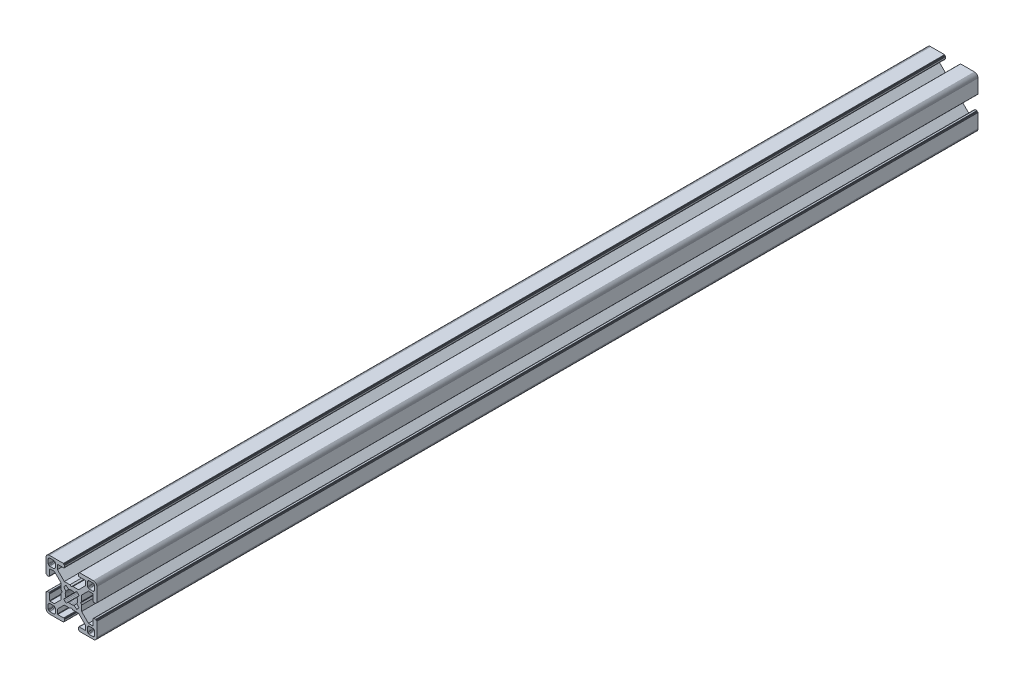
SolidWorks part; units mm, degrees
ref_plane "Front Plane" through (0, 0, 0) normal (0, 0, 1) x (1, 0, 0)
ref_plane "Top Plane" through (0, 0, 0) normal (0, 1, 0) x (1, 0, 0)
ref_plane "Right Plane" through (0, 0, 0) normal (1, 0, 0) x (0, 0, -1)
ref_plane "Plane1" through (0, 0, 0) normal (0, 0, 1) x (1, 0, 0)
sketch "Sketch1" plane through (0, 0, 0) normal (0, 0, 1) x (1, 0, 0)
  line L0 (28.3473, 29.9696) -> (28, 30)
  line L1 (28, 30) -> (19.75, 30)
  line L2 (19.75, 30) -> (19.7153, 29.997)
  line L3 (19.7153, 29.997) -> (19.6816, 29.9879)
  line L4 (19.6816, 29.9879) -> (19.65, 29.9732)
  line L5 (19.65, 29.9732) -> (19.6214, 29.9532)
  line L6 (19.6214, 29.9532) -> (19.5968, 29.9286)
  line L7 (19.5968, 29.9286) -> (19.5768, 29.9)
  line L8 (19.5768, 29.9) -> (19.5621, 29.8684)
  line L9 (19.5621, 29.8684) -> (19.553, 29.8347)
  line L10 (19.553, 29.8347) -> (19.55, 29.8)
  line L11 (19.55, 29.8) -> (19.55, 29.7)
  line L12 (19.55, 29.7) -> (19.547, 29.6653)
  line L13 (19.547, 29.6653) -> (19.5379, 29.6316)
  line L14 (19.5379, 29.6316) -> (19.5232, 29.6)
  line L15 (19.5232, 29.6) -> (19.5032, 29.5714)
  line L16 (19.5032, 29.5714) -> (19.4786, 29.5468)
  line L17 (19.4786, 29.5468) -> (19.45, 29.5268)
  line L18 (19.45, 29.5268) -> (19.4184, 29.5121)
  line L19 (19.4184, 29.5121) -> (19.3847, 29.503)
  line L20 (19.3847, 29.503) -> (19.35, 29.5)
  line L21 (19.35, 29.5) -> (19.25, 29.5)
  line L22 (19.25, 29.5) -> (19.2153, 29.497)
  line L23 (19.2153, 29.497) -> (19.1816, 29.4879)
  line L24 (19.1816, 29.4879) -> (19.15, 29.4732)
  line L25 (19.15, 29.4732) -> (19.1214, 29.4532)
  line L26 (19.1214, 29.4532) -> (19.0968, 29.4286)
  line L27 (19.0968, 29.4286) -> (19.0768, 29.4)
  line L28 (19.0768, 29.4) -> (19.0621, 29.3684)
  line L29 (19.0621, 29.3684) -> (19.053, 29.3347)
  line L30 (19.053, 29.3347) -> (19.05, 29.3)
  line L31 (19.05, 29.3) -> (19.05, 28.4)
  line L32 (19.05, 28.4) -> (19.0591, 28.2958)
  line L33 (19.0591, 28.2958) -> (19.0862, 28.1948)
  line L34 (19.0862, 28.1948) -> (19.1304, 28.1)
  line L35 (19.1304, 28.1) -> (19.1904, 28.0143)
  line L36 (19.1904, 28.0143) -> (19.2643, 27.9404)
  line L37 (19.2643, 27.9404) -> (19.35, 27.8804)
  line L38 (19.35, 27.8804) -> (19.4448, 27.8362)
  line L39 (19.4448, 27.8362) -> (19.5458, 27.8091)
  line L40 (19.5458, 27.8091) -> (19.65, 27.8)
  line L41 (19.65, 27.8) -> (23.05, 27.8)
  line L42 (23.05, 27.8) -> (23.0847, 27.7969)
  line L43 (23.0847, 27.7969) -> (23.1184, 27.7879)
  line L44 (23.1184, 27.7879) -> (23.15, 27.7732)
  line L45 (23.15, 27.7732) -> (23.1786, 27.7532)
  line L46 (23.1786, 27.7532) -> (23.2032, 27.7285)
  line L47 (23.2032, 27.7285) -> (23.2232, 27.7)
  line L48 (23.2232, 27.7) -> (23.2379, 27.6684)
  line L49 (23.2379, 27.6684) -> (23.247, 27.6347)
  line L50 (23.247, 27.6347) -> (23.25, 27.6)
  line L51 (23.25, 27.6) -> (23.25, 25.05)
  line L52 (23.25, 25.05) -> (19.2045, 21)
  line L53 (19.2045, 21) -> (15.9, 21)
  line L54 (15.9, 21) -> (15, 20.4848)
  line L55 (15, 20.4848) -> (14.1, 21)
  line L56 (14.1, 21) -> (10.7955, 21)
  line L57 (10.7955, 21) -> (7.9973, 23.8013)
  line L58 (7.9973, 23.8013) -> (6.75, 25.05)
  line L59 (6.75, 25.05) -> (6.75, 27.6)
  line L60 (6.75, 27.6) -> (6.753, 27.6347)
  line L61 (6.753, 27.6347) -> (6.7621, 27.6684)
  line L62 (6.7621, 27.6684) -> (6.7768, 27.7)
  line L63 (6.7768, 27.7) -> (6.7968, 27.7285)
  line L64 (6.7968, 27.7285) -> (6.8215, 27.7532)
  line L65 (6.8215, 27.7532) -> (6.85, 27.7732)
  line L66 (6.85, 27.7732) -> (6.8816, 27.7879)
  line L67 (6.8816, 27.7879) -> (6.9153, 27.7969)
  line L68 (6.9153, 27.7969) -> (6.95, 27.8)
  line L69 (6.95, 27.8) -> (10.35, 27.8)
  line L70 (10.35, 27.8) -> (10.4542, 27.8091)
  line L71 (10.4542, 27.8091) -> (10.5552, 27.8362)
  line L72 (10.5552, 27.8362) -> (10.65, 27.8804)
  line L73 (10.65, 27.8804) -> (10.7357, 27.9404)
  line L74 (10.7357, 27.9404) -> (10.8096, 28.0143)
  line L75 (10.8096, 28.0143) -> (10.8696, 28.1)
  line L76 (10.8696, 28.1) -> (10.9138, 28.1948)
  line L77 (10.9138, 28.1948) -> (10.9409, 28.2958)
  line L78 (10.9409, 28.2958) -> (10.95, 28.4)
  line L79 (10.95, 28.4) -> (10.95, 29.3)
  line L80 (10.95, 29.3) -> (10.947, 29.3347)
  line L81 (10.947, 29.3347) -> (10.938, 29.3684)
  line L82 (10.938, 29.3684) -> (10.9232, 29.4)
  line L83 (10.9232, 29.4) -> (10.9032, 29.4286)
  line L84 (10.9032, 29.4286) -> (10.8786, 29.4532)
  line L85 (10.8786, 29.4532) -> (10.85, 29.4732)
  line L86 (10.85, 29.4732) -> (10.8184, 29.4879)
  line L87 (10.8184, 29.4879) -> (10.7847, 29.497)
  line L88 (10.7847, 29.497) -> (10.75, 29.5)
  line L89 (10.75, 29.5) -> (10.65, 29.5)
  line L90 (10.65, 29.5) -> (10.6153, 29.503)
  line L91 (10.6153, 29.503) -> (10.5816, 29.5121)
  line L92 (10.5816, 29.5121) -> (10.55, 29.5268)
  line L93 (10.55, 29.5268) -> (10.5214, 29.5468)
  line L94 (10.5214, 29.5468) -> (10.4968, 29.5714)
  line L95 (10.4968, 29.5714) -> (10.4768, 29.6)
  line L96 (10.4768, 29.6) -> (10.4621, 29.6316)
  line L97 (10.4621, 29.6316) -> (10.453, 29.6653)
  line L98 (10.453, 29.6653) -> (10.45, 29.7)
  line L99 (10.45, 29.7) -> (10.45, 29.8)
  line L100 (10.45, 29.8) -> (10.447, 29.8347)
  line L101 (10.447, 29.8347) -> (10.4379, 29.8684)
  line L102 (10.4379, 29.8684) -> (10.4232, 29.9)
  line L103 (10.4232, 29.9) -> (10.4032, 29.9286)
  line L104 (10.4032, 29.9286) -> (10.3786, 29.9532)
  line L105 (10.3786, 29.9532) -> (10.35, 29.9732)
  line L106 (10.35, 29.9732) -> (10.3184, 29.9879)
  line L107 (10.3184, 29.9879) -> (10.2847, 29.997)
  line L108 (10.2847, 29.997) -> (10.25, 30)
  line L109 (10.25, 30) -> (2, 30)
  line L110 (2, 30) -> (1.6527, 29.9696)
  line L111 (1.6527, 29.9696) -> (1.316, 29.8794)
  line L112 (1.316, 29.8794) -> (1, 29.7321)
  line L113 (1, 29.7321) -> (0.7144, 29.5321)
  line L114 (0.7144, 29.5321) -> (0.4679, 29.2856)
  line L115 (0.4679, 29.2856) -> (0.2679, 29)
  line L116 (0.2679, 29) -> (0.1206, 28.684)
  line L117 (0.1206, 28.684) -> (0.0304, 28.3473)
  line L118 (0.0304, 28.3473) -> (0, 28)
  line L119 (0, 28) -> (0, 19.75)
  line L120 (0, 19.75) -> (0.003, 19.7153)
  line L121 (0.003, 19.7153) -> (0.0121, 19.6816)
  line L122 (0.0121, 19.6816) -> (0.0268, 19.65)
  line L123 (0.0268, 19.65) -> (0.0468, 19.6214)
  line L124 (0.0468, 19.6214) -> (0.0714, 19.5968)
  line L125 (0.0714, 19.5968) -> (0.1, 19.5768)
  line L126 (0.1, 19.5768) -> (0.1316, 19.5621)
  line L127 (0.1316, 19.5621) -> (0.1653, 19.553)
  line L128 (0.1653, 19.553) -> (0.2, 19.55)
  line L129 (0.2, 19.55) -> (0.3, 19.55)
  line L130 (0.3, 19.55) -> (0.3347, 19.547)
  line L131 (0.3347, 19.547) -> (0.3684, 19.5379)
  line L132 (0.3684, 19.5379) -> (0.4, 19.5232)
  line L133 (0.4, 19.5232) -> (0.4286, 19.5032)
  line L134 (0.4286, 19.5032) -> (0.4532, 19.4786)
  line L135 (0.4532, 19.4786) -> (0.4732, 19.45)
  line L136 (0.4732, 19.45) -> (0.4879, 19.4184)
  line L137 (0.4879, 19.4184) -> (0.497, 19.3847)
  line L138 (0.497, 19.3847) -> (0.5, 19.35)
  line L139 (0.5, 19.35) -> (0.5, 19.25)
  line L140 (0.5, 19.25) -> (0.503, 19.2153)
  line L141 (0.503, 19.2153) -> (0.5121, 19.1816)
  line L142 (0.5121, 19.1816) -> (0.5268, 19.15)
  line L143 (0.5268, 19.15) -> (0.5468, 19.1214)
  line L144 (0.5468, 19.1214) -> (0.5714, 19.0968)
  line L145 (0.5714, 19.0968) -> (0.6, 19.0768)
  line L146 (0.6, 19.0768) -> (0.6316, 19.0621)
  line L147 (0.6316, 19.0621) -> (0.6653, 19.053)
  line L148 (0.6653, 19.053) -> (0.7, 19.05)
  line L149 (0.7, 19.05) -> (1.6, 19.05)
  line L150 (1.6, 19.05) -> (1.7042, 19.0591)
  line L151 (1.7042, 19.0591) -> (1.8052, 19.0862)
  line L152 (1.8052, 19.0862) -> (1.9, 19.1304)
  line L153 (1.9, 19.1304) -> (1.9857, 19.1904)
  line L154 (1.9857, 19.1904) -> (2.0596, 19.2643)
  line L155 (2.0596, 19.2643) -> (2.1196, 19.35)
  line L156 (2.1196, 19.35) -> (2.1638, 19.4448)
  line L157 (2.1638, 19.4448) -> (2.1909, 19.5458)
  line L158 (2.1909, 19.5458) -> (2.2, 19.65)
  line L159 (2.2, 19.65) -> (2.2, 23.05)
  line L160 (2.2, 23.05) -> (2.203, 23.0847)
  line L161 (2.203, 23.0847) -> (2.2121, 23.1184)
  line L162 (2.2121, 23.1184) -> (2.2268, 23.15)
  line L163 (2.2268, 23.15) -> (2.2468, 23.1786)
  line L164 (2.2468, 23.1786) -> (2.2714, 23.2032)
  line L165 (2.2714, 23.2032) -> (2.3, 23.2232)
  line L166 (2.3, 23.2232) -> (2.3316, 23.2379)
  line L167 (2.3316, 23.2379) -> (2.3653, 23.247)
  line L168 (2.3653, 23.247) -> (2.4, 23.25)
  line L169 (2.4, 23.25) -> (4.95, 23.25)
  line L170 (4.95, 23.25) -> (7.9973, 20.2027)
  line L171 (7.9973, 20.2027) -> (8.9955, 19.2045)
  line L172 (8.9955, 19.2045) -> (8.9955, 15.9)
  line L173 (8.9955, 15.9) -> (9.5151, 15)
  line L174 (9.5151, 15) -> (8.9955, 14.1)
  line L175 (8.9955, 14.1) -> (8.9955, 10.7955)
  line L176 (8.9955, 10.7955) -> (4.95, 6.75)
  line L177 (4.95, 6.75) -> (2.4, 6.75)
  line L178 (2.4, 6.75) -> (2.3653, 6.753)
  line L179 (2.3653, 6.753) -> (2.3316, 6.7621)
  line L180 (2.3316, 6.7621) -> (2.3, 6.7768)
  line L181 (2.3, 6.7768) -> (2.2714, 6.7968)
  line L182 (2.2714, 6.7968) -> (2.2468, 6.8214)
  line L183 (2.2468, 6.8214) -> (2.2268, 6.85)
  line L184 (2.2268, 6.85) -> (2.2121, 6.8816)
  line L185 (2.2121, 6.8816) -> (2.203, 6.9153)
  line L186 (2.203, 6.9153) -> (2.2, 6.95)
  line L187 (2.2, 6.95) -> (2.2, 10.35)
  line L188 (2.2, 10.35) -> (2.1909, 10.4542)
  line L189 (2.1909, 10.4542) -> (2.1638, 10.5552)
  line L190 (2.1638, 10.5552) -> (2.1196, 10.65)
  line L191 (2.1196, 10.65) -> (2.0596, 10.7357)
  line L192 (2.0596, 10.7357) -> (1.9857, 10.8096)
  line L193 (1.9857, 10.8096) -> (1.9, 10.8696)
  line L194 (1.9, 10.8696) -> (1.8052, 10.9138)
  line L195 (1.8052, 10.9138) -> (1.7042, 10.9409)
  line L196 (1.7042, 10.9409) -> (1.6, 10.95)
  line L197 (1.6, 10.95) -> (0.7, 10.95)
  line L198 (0.7, 10.95) -> (0.6653, 10.9469)
  line L199 (0.6653, 10.9469) -> (0.6316, 10.9379)
  line L200 (0.6316, 10.9379) -> (0.6, 10.9232)
  line L201 (0.6, 10.9232) -> (0.5715, 10.9032)
  line L202 (0.5715, 10.9032) -> (0.5468, 10.8785)
  line L203 (0.5468, 10.8785) -> (0.5268, 10.85)
  line L204 (0.5268, 10.85) -> (0.5121, 10.8184)
  line L205 (0.5121, 10.8184) -> (0.503, 10.7847)
  line L206 (0.503, 10.7847) -> (0.5, 10.75)
  line L207 (0.5, 10.75) -> (0.5, 10.65)
  line L208 (0.5, 10.65) -> (0.497, 10.6153)
  line L209 (0.497, 10.6153) -> (0.4879, 10.5816)
  line L210 (0.4879, 10.5816) -> (0.4732, 10.55)
  line L211 (0.4732, 10.55) -> (0.4532, 10.5214)
  line L212 (0.4532, 10.5214) -> (0.4286, 10.4968)
  line L213 (0.4286, 10.4968) -> (0.4, 10.4768)
  line L214 (0.4, 10.4768) -> (0.3684, 10.4621)
  line L215 (0.3684, 10.4621) -> (0.3347, 10.453)
  line L216 (0.3347, 10.453) -> (0.3, 10.45)
  line L217 (0.3, 10.45) -> (0.2, 10.45)
  line L218 (0.2, 10.45) -> (0.1653, 10.447)
  line L219 (0.1653, 10.447) -> (0.1316, 10.4379)
  line L220 (0.1316, 10.4379) -> (0.1, 10.4232)
  line L221 (0.1, 10.4232) -> (0.0714, 10.4032)
  line L222 (0.0714, 10.4032) -> (0.0468, 10.3786)
  line L223 (0.0468, 10.3786) -> (0.0268, 10.35)
  line L224 (0.0268, 10.35) -> (0.0121, 10.3184)
  line L225 (0.0121, 10.3184) -> (0.003, 10.2847)
  line L226 (0.003, 10.2847) -> (0, 10.25)
  line L227 (0, 10.25) -> (0, 2)
  line L228 (0, 2) -> (0.0304, 1.6527)
  line L229 (0.0304, 1.6527) -> (0.1206, 1.316)
  line L230 (0.1206, 1.316) -> (0.2679, 1)
  line L231 (0.2679, 1) -> (0.4679, 0.7144)
  line L232 (0.4679, 0.7144) -> (0.7144, 0.4679)
  line L233 (0.7144, 0.4679) -> (1, 0.2679)
  line L234 (1, 0.2679) -> (1.316, 0.1206)
  line L235 (1.316, 0.1206) -> (1.6527, 0.0304)
  line L236 (1.6527, 0.0304) -> (2, 0)
  line L237 (2, 0) -> (10.25, 0)
  line L238 (10.25, 0) -> (10.2847, 0.003)
  line L239 (10.2847, 0.003) -> (10.3184, 0.0121)
  line L240 (10.3184, 0.0121) -> (10.35, 0.0268)
  line L241 (10.35, 0.0268) -> (10.3786, 0.0468)
  line L242 (10.3786, 0.0468) -> (10.4032, 0.0714)
  line L243 (10.4032, 0.0714) -> (10.4232, 0.1)
  line L244 (10.4232, 0.1) -> (10.4379, 0.1316)
  line L245 (10.4379, 0.1316) -> (10.447, 0.1653)
  line L246 (10.447, 0.1653) -> (10.45, 0.2)
  line L247 (10.45, 0.2) -> (10.45, 0.3)
  line L248 (10.45, 0.3) -> (10.453, 0.3347)
  line L249 (10.453, 0.3347) -> (10.4621, 0.3684)
  line L250 (10.4621, 0.3684) -> (10.4768, 0.4)
  line L251 (10.4768, 0.4) -> (10.4968, 0.4286)
  line L252 (10.4968, 0.4286) -> (10.5214, 0.4532)
  line L253 (10.5214, 0.4532) -> (10.55, 0.4732)
  line L254 (10.55, 0.4732) -> (10.5816, 0.4879)
  line L255 (10.5816, 0.4879) -> (10.6153, 0.497)
  line L256 (10.6153, 0.497) -> (10.65, 0.5)
  line L257 (10.65, 0.5) -> (10.75, 0.5)
  line L258 (10.75, 0.5) -> (10.7847, 0.503)
  line L259 (10.7847, 0.503) -> (10.8184, 0.5121)
  line L260 (10.8184, 0.5121) -> (10.85, 0.5268)
  line L261 (10.85, 0.5268) -> (10.8785, 0.5468)
  line L262 (10.8785, 0.5468) -> (10.9032, 0.5715)
  line L263 (10.9032, 0.5715) -> (10.9232, 0.6)
  line L264 (10.9232, 0.6) -> (10.9379, 0.6316)
  line L265 (10.9379, 0.6316) -> (10.9469, 0.6653)
  line L266 (10.9469, 0.6653) -> (10.95, 0.7)
  line L267 (10.95, 0.7) -> (10.95, 1.6)
  line L268 (10.95, 1.6) -> (10.9409, 1.7042)
  line L269 (10.9409, 1.7042) -> (10.9138, 1.8052)
  line L270 (10.9138, 1.8052) -> (10.8696, 1.9)
  line L271 (10.8696, 1.9) -> (10.8096, 1.9857)
  line L272 (10.8096, 1.9857) -> (10.7357, 2.0596)
  line L273 (10.7357, 2.0596) -> (10.65, 2.1196)
  line L274 (10.65, 2.1196) -> (10.5552, 2.1638)
  line L275 (10.5552, 2.1638) -> (10.4542, 2.1909)
  line L276 (10.4542, 2.1909) -> (10.35, 2.2)
  line L277 (10.35, 2.2) -> (6.95, 2.2)
  line L278 (6.95, 2.2) -> (6.9153, 2.203)
  line L279 (6.9153, 2.203) -> (6.8816, 2.212)
  line L280 (6.8816, 2.212) -> (6.85, 2.2268)
  line L281 (6.85, 2.2268) -> (6.8215, 2.2468)
  line L282 (6.8215, 2.2468) -> (6.7968, 2.2714)
  line L283 (6.7968, 2.2714) -> (6.7768, 2.3)
  line L284 (6.7768, 2.3) -> (6.7621, 2.3316)
  line L285 (6.7621, 2.3316) -> (6.753, 2.3653)
  line L286 (6.753, 2.3653) -> (6.75, 2.4)
  line L287 (6.75, 2.4) -> (6.75, 4.95)
  line L288 (6.75, 4.95) -> (9.7875, 7.9908)
  line L289 (9.7875, 7.9908) -> (10.7955, 9)
  line L290 (10.7955, 9) -> (14.1, 9)
  line L291 (14.1, 9) -> (15, 9.5151)
  line L292 (15, 9.5151) -> (15.9, 9)
  line L293 (15.9, 9) -> (19.2045, 9)
  line L294 (19.2045, 9) -> (20.2126, 7.9908)
  line L295 (20.2126, 7.9908) -> (23.25, 4.95)
  line L296 (23.25, 4.95) -> (23.25, 2.4)
  line L297 (23.25, 2.4) -> (23.247, 2.3653)
  line L298 (23.247, 2.3653) -> (23.2379, 2.3316)
  line L299 (23.2379, 2.3316) -> (23.2232, 2.3)
  line L300 (23.2232, 2.3) -> (23.2032, 2.2714)
  line L301 (23.2032, 2.2714) -> (23.1786, 2.2468)
  line L302 (23.1786, 2.2468) -> (23.15, 2.2268)
  line L303 (23.15, 2.2268) -> (23.1184, 2.212)
  line L304 (23.1184, 2.212) -> (23.0847, 2.203)
  line L305 (23.0847, 2.203) -> (23.05, 2.2)
  line L306 (23.05, 2.2) -> (19.65, 2.2)
  line L307 (19.65, 2.2) -> (19.5458, 2.1909)
  line L308 (19.5458, 2.1909) -> (19.4448, 2.1638)
  line L309 (19.4448, 2.1638) -> (19.35, 2.1196)
  line L310 (19.35, 2.1196) -> (19.2643, 2.0596)
  line L311 (19.2643, 2.0596) -> (19.1904, 1.9857)
  line L312 (19.1904, 1.9857) -> (19.1304, 1.9)
  line L313 (19.1304, 1.9) -> (19.0862, 1.8052)
  line L314 (19.0862, 1.8052) -> (19.0591, 1.7042)
  line L315 (19.0591, 1.7042) -> (19.05, 1.6)
  line L316 (19.05, 1.6) -> (19.05, 0.7)
  line L317 (19.05, 0.7) -> (19.053, 0.6653)
  line L318 (19.053, 0.6653) -> (19.0621, 0.6316)
  line L319 (19.0621, 0.6316) -> (19.0768, 0.6)
  line L320 (19.0768, 0.6) -> (19.0968, 0.5714)
  line L321 (19.0968, 0.5714) -> (19.1214, 0.5468)
  line L322 (19.1214, 0.5468) -> (19.15, 0.5268)
  line L323 (19.15, 0.5268) -> (19.1816, 0.5121)
  line L324 (19.1816, 0.5121) -> (19.2153, 0.503)
  line L325 (19.2153, 0.503) -> (19.25, 0.5)
  line L326 (19.25, 0.5) -> (19.35, 0.5)
  line L327 (19.35, 0.5) -> (19.3847, 0.497)
  line L328 (19.3847, 0.497) -> (19.4184, 0.4879)
  line L329 (19.4184, 0.4879) -> (19.45, 0.4732)
  line L330 (19.45, 0.4732) -> (19.4786, 0.4532)
  line L331 (19.4786, 0.4532) -> (19.5032, 0.4286)
  line L332 (19.5032, 0.4286) -> (19.5232, 0.4)
  line L333 (19.5232, 0.4) -> (19.5379, 0.3684)
  line L334 (19.5379, 0.3684) -> (19.547, 0.3347)
  line L335 (19.547, 0.3347) -> (19.55, 0.3)
  line L336 (19.55, 0.3) -> (19.55, 0.2)
  line L337 (19.55, 0.2) -> (19.553, 0.1653)
  line L338 (19.553, 0.1653) -> (19.5621, 0.1316)
  line L339 (19.5621, 0.1316) -> (19.5768, 0.1)
  line L340 (19.5768, 0.1) -> (19.5968, 0.0714)
  line L341 (19.5968, 0.0714) -> (19.6214, 0.0468)
  line L342 (19.6214, 0.0468) -> (19.65, 0.0268)
  line L343 (19.65, 0.0268) -> (19.6816, 0.0121)
  line L344 (19.6816, 0.0121) -> (19.7153, 0.003)
  line L345 (19.7153, 0.003) -> (19.75, 0)
  line L346 (19.75, 0) -> (28, 0)
  line L347 (28, 0) -> (28.3473, 0.0304)
  line L348 (28.3473, 0.0304) -> (28.684, 0.1206)
  line L349 (28.684, 0.1206) -> (29, 0.2679)
  line L350 (29, 0.2679) -> (29.2856, 0.4679)
  line L351 (29.2856, 0.4679) -> (29.5321, 0.7144)
  line L352 (29.5321, 0.7144) -> (29.7321, 1)
  line L353 (29.7321, 1) -> (29.8794, 1.316)
  line L354 (29.8794, 1.316) -> (29.9696, 1.6527)
  line L355 (29.9696, 1.6527) -> (30, 2)
  line L356 (30, 2) -> (30, 10.25)
  line L357 (30, 10.25) -> (29.997, 10.2847)
  line L358 (29.997, 10.2847) -> (29.988, 10.3184)
  line L359 (29.988, 10.3184) -> (29.9732, 10.35)
  line L360 (29.9732, 10.35) -> (29.9532, 10.3785)
  line L361 (29.9532, 10.3785) -> (29.9286, 10.4032)
  line L362 (29.9286, 10.4032) -> (29.9, 10.4232)
  line L363 (29.9, 10.4232) -> (29.8684, 10.4379)
  line L364 (29.8684, 10.4379) -> (29.8347, 10.447)
  line L365 (29.8347, 10.447) -> (29.8, 10.45)
  line L366 (29.8, 10.45) -> (29.7, 10.45)
  line L367 (29.7, 10.45) -> (29.6649, 10.4534)
  line L368 (29.6649, 10.4534) -> (29.6312, 10.4624)
  line L369 (29.6312, 10.4624) -> (29.5996, 10.4772)
  line L370 (29.5996, 10.4772) -> (29.5711, 10.4972)
  line L371 (29.5711, 10.4972) -> (29.5464, 10.5218)
  line L372 (29.5464, 10.5218) -> (29.5264, 10.5504)
  line L373 (29.5264, 10.5504) -> (29.5117, 10.582)
  line L374 (29.5117, 10.582) -> (29.5027, 10.6156)
  line L375 (29.5027, 10.6156) -> (29.4996, 10.6504)
  line L376 (29.4996, 10.6504) -> (29.4996, 10.7504)
  line L377 (29.4996, 10.7504) -> (29.497, 10.7847)
  line L378 (29.497, 10.7847) -> (29.4879, 10.8184)
  line L379 (29.4879, 10.8184) -> (29.4732, 10.85)
  line L380 (29.4732, 10.85) -> (29.4532, 10.8785)
  line L381 (29.4532, 10.8785) -> (29.4286, 10.9032)
  line L382 (29.4286, 10.9032) -> (29.4, 10.9232)
  line L383 (29.4, 10.9232) -> (29.3684, 10.9379)
  line L384 (29.3684, 10.9379) -> (29.3347, 10.9469)
  line L385 (29.3347, 10.9469) -> (29.3, 10.95)
  line L386 (29.3, 10.95) -> (28.4, 10.95)
  line L387 (28.4, 10.95) -> (28.2958, 10.9409)
  line L388 (28.2958, 10.9409) -> (28.1948, 10.9138)
  line L389 (28.1948, 10.9138) -> (28.1, 10.8696)
  line L390 (28.1, 10.8696) -> (28.0143, 10.8096)
  line L391 (28.0143, 10.8096) -> (27.9404, 10.7357)
  line L392 (27.9404, 10.7357) -> (27.8804, 10.65)
  line L393 (27.8804, 10.65) -> (27.8362, 10.5552)
  line L394 (27.8362, 10.5552) -> (27.8091, 10.4542)
  line L395 (27.8091, 10.4542) -> (27.8, 10.35)
  line L396 (27.8, 10.35) -> (27.8, 6.95)
  line L397 (27.8, 6.95) -> (27.797, 6.9153)
  line L398 (27.797, 6.9153) -> (27.7879, 6.8816)
  line L399 (27.7879, 6.8816) -> (27.7732, 6.85)
  line L400 (27.7732, 6.85) -> (27.7532, 6.8214)
  line L401 (27.7532, 6.8214) -> (27.7286, 6.7968)
  line L402 (27.7286, 6.7968) -> (27.7, 6.7768)
  line L403 (27.7, 6.7768) -> (27.6684, 6.7621)
  line L404 (27.6684, 6.7621) -> (27.6347, 6.753)
  line L405 (27.6347, 6.753) -> (27.6, 6.75)
  line L406 (27.6, 6.75) -> (25.05, 6.75)
  line L407 (25.05, 6.75) -> (23.8092, 7.9908)
  line L408 (23.8092, 7.9908) -> (21.0045, 10.7955)
  line L409 (21.0045, 10.7955) -> (21.0045, 14.1)
  line L410 (21.0045, 14.1) -> (20.4849, 15)
  line L411 (20.4849, 15) -> (21.0045, 15.9)
  line L412 (21.0045, 15.9) -> (21.0045, 19.2045)
  line L413 (21.0045, 19.2045) -> (25.05, 23.25)
  line L414 (25.05, 23.25) -> (27.6, 23.25)
  line L415 (27.6, 23.25) -> (27.6347, 23.247)
  line L416 (27.6347, 23.247) -> (27.6684, 23.2379)
  line L417 (27.6684, 23.2379) -> (27.7, 23.2232)
  line L418 (27.7, 23.2232) -> (27.7286, 23.2032)
  line L419 (27.7286, 23.2032) -> (27.7532, 23.1786)
  line L420 (27.7532, 23.1786) -> (27.7732, 23.15)
  line L421 (27.7732, 23.15) -> (27.7879, 23.1184)
  line L422 (27.7879, 23.1184) -> (27.797, 23.0847)
  line L423 (27.797, 23.0847) -> (27.8, 23.05)
  line L424 (27.8, 23.05) -> (27.8, 19.65)
  line L425 (27.8, 19.65) -> (27.8091, 19.5458)
  line L426 (27.8091, 19.5458) -> (27.8362, 19.4448)
  line L427 (27.8362, 19.4448) -> (27.8804, 19.35)
  line L428 (27.8804, 19.35) -> (27.9404, 19.2643)
  line L429 (27.9404, 19.2643) -> (28.0143, 19.1904)
  line L430 (28.0143, 19.1904) -> (28.1, 19.1304)
  line L431 (28.1, 19.1304) -> (28.1948, 19.0862)
  line L432 (28.1948, 19.0862) -> (28.2958, 19.0591)
  line L433 (28.2958, 19.0591) -> (28.4, 19.05)
  line L434 (28.4, 19.05) -> (29.3, 19.05)
  line L435 (29.3, 19.05) -> (29.3347, 19.053)
  line L436 (29.3347, 19.053) -> (29.3684, 19.0621)
  line L437 (29.3684, 19.0621) -> (29.4, 19.0768)
  line L438 (29.4, 19.0768) -> (29.4282, 19.0971)
  line L439 (29.4282, 19.0971) -> (29.4528, 19.1218)
  line L440 (29.4528, 19.1218) -> (29.4728, 19.1504)
  line L441 (29.4728, 19.1504) -> (29.4876, 19.182)
  line L442 (29.4876, 19.182) -> (29.4966, 19.2156)
  line L443 (29.4966, 19.2156) -> (29.4996, 19.2504)
  line L444 (29.4996, 19.2504) -> (29.4996, 19.3504)
  line L445 (29.4996, 19.3504) -> (29.5027, 19.3851)
  line L446 (29.5027, 19.3851) -> (29.5117, 19.4188)
  line L447 (29.5117, 19.4188) -> (29.5264, 19.4504)
  line L448 (29.5264, 19.4504) -> (29.5464, 19.4789)
  line L449 (29.5464, 19.4789) -> (29.5711, 19.5036)
  line L450 (29.5711, 19.5036) -> (29.5996, 19.5236)
  line L451 (29.5996, 19.5236) -> (29.6312, 19.5383)
  line L452 (29.6312, 19.5383) -> (29.6649, 19.5473)
  line L453 (29.6649, 19.5473) -> (29.7, 19.55)
  line L454 (29.7, 19.55) -> (29.8, 19.55)
  line L455 (29.8, 19.55) -> (29.8347, 19.553)
  line L456 (29.8347, 19.553) -> (29.8684, 19.5621)
  line L457 (29.8684, 19.5621) -> (29.9, 19.5768)
  line L458 (29.9, 19.5768) -> (29.9286, 19.5968)
  line L459 (29.9286, 19.5968) -> (29.9532, 19.6214)
  line L460 (29.9532, 19.6214) -> (29.9732, 19.65)
  line L461 (29.9732, 19.65) -> (29.9879, 19.6816)
  line L462 (29.9879, 19.6816) -> (29.997, 19.7153)
  line L463 (29.997, 19.7153) -> (30, 19.75)
  line L464 (30, 19.75) -> (30, 28)
  line L465 (30, 28) -> (29.9696, 28.3473)
  line L466 (29.9696, 28.3473) -> (29.8794, 28.684)
  line L467 (29.8794, 28.684) -> (29.7321, 29)
  line L468 (29.7321, 29) -> (29.5321, 29.2856)
  line L469 (29.5321, 29.2856) -> (29.2856, 29.5321)
  line L470 (29.2856, 29.5321) -> (29, 29.7321)
  line L471 (29, 29.7321) -> (28.684, 29.8794)
  line L472 (28.684, 29.8794) -> (28.3473, 29.9696)
  line L473 (1.3, 25.5) -> (1.3, 27.7)
  line L474 (1.3, 27.7) -> (1.3123, 27.8564)
  line L475 (1.3123, 27.8564) -> (1.3489, 28.009)
  line L476 (1.3489, 28.009) -> (1.409, 28.154)
  line L477 (1.409, 28.154) -> (1.491, 28.2878)
  line L478 (1.491, 28.2878) -> (1.5929, 28.4071)
  line L479 (1.5929, 28.4071) -> (1.7122, 28.509)
  line L480 (1.7122, 28.509) -> (1.846, 28.591)
  line L481 (1.846, 28.591) -> (1.991, 28.6511)
  line L482 (1.991, 28.6511) -> (2.1436, 28.6877)
  line L483 (2.1436, 28.6877) -> (2.3, 28.7)
  line L484 (2.3, 28.7) -> (4.5, 28.7)
  line L485 (4.5, 28.7) -> (4.6564, 28.6877)
  line L486 (4.6564, 28.6877) -> (4.809, 28.6511)
  line L487 (4.809, 28.6511) -> (4.954, 28.591)
  line L488 (4.954, 28.591) -> (5.0878, 28.509)
  line L489 (5.0878, 28.509) -> (5.2071, 28.4071)
  line L490 (5.2071, 28.4071) -> (5.309, 28.2878)
  line L491 (5.309, 28.2878) -> (5.391, 28.154)
  line L492 (5.391, 28.154) -> (5.4511, 28.009)
  line L493 (5.4511, 28.009) -> (5.4877, 27.8564)
  line L494 (5.4877, 27.8564) -> (5.5, 27.7)
  line L495 (5.5, 27.7) -> (5.5, 25.5)
  line L496 (5.5, 25.5) -> (5.4877, 25.3436)
  line L497 (5.4877, 25.3436) -> (5.4511, 25.191)
  line L498 (5.4511, 25.191) -> (5.391, 25.046)
  line L499 (5.391, 25.046) -> (5.309, 24.9122)
  line L500 (5.309, 24.9122) -> (5.2071, 24.7929)
  line L501 (5.2071, 24.7929) -> (5.0878, 24.691)
  line L502 (5.0878, 24.691) -> (4.954, 24.609)
  line L503 (4.954, 24.609) -> (4.809, 24.5489)
  line L504 (4.809, 24.5489) -> (4.6564, 24.5123)
  line L505 (4.6564, 24.5123) -> (4.5, 24.5)
  line L506 (4.5, 24.5) -> (2.3, 24.5)
  line L507 (2.3, 24.5) -> (2.1436, 24.5123)
  line L508 (2.1436, 24.5123) -> (1.991, 24.5489)
  line L509 (1.991, 24.5489) -> (1.846, 24.609)
  line L510 (1.846, 24.609) -> (1.7122, 24.691)
  line L511 (1.7122, 24.691) -> (1.5929, 24.7929)
  line L512 (1.5929, 24.7929) -> (1.491, 24.9122)
  line L513 (1.491, 24.9122) -> (1.409, 25.046)
  line L514 (1.409, 25.046) -> (1.3489, 25.191)
  line L515 (1.3489, 25.191) -> (1.3123, 25.3436)
  line L516 (1.3123, 25.3436) -> (1.3, 25.5)
  line L517 (25.3436, 28.6877) -> (25.5, 28.7)
  line L518 (25.5, 28.7) -> (27.7, 28.7)
  line L519 (27.7, 28.7) -> (27.8564, 28.6877)
  line L520 (27.8564, 28.6877) -> (28.009, 28.6511)
  line L521 (28.009, 28.6511) -> (28.154, 28.591)
  line L522 (28.154, 28.591) -> (28.2878, 28.509)
  line L523 (28.2878, 28.509) -> (28.4071, 28.4071)
  line L524 (28.4071, 28.4071) -> (28.509, 28.2878)
  line L525 (28.509, 28.2878) -> (28.591, 28.154)
  line L526 (28.591, 28.154) -> (28.6511, 28.009)
  line L527 (28.6511, 28.009) -> (28.6877, 27.8564)
  line L528 (28.6877, 27.8564) -> (28.7, 27.7)
  line L529 (28.7, 27.7) -> (28.7, 25.5)
  line L530 (28.7, 25.5) -> (28.6877, 25.3436)
  line L531 (28.6877, 25.3436) -> (28.6511, 25.191)
  line L532 (28.6511, 25.191) -> (28.591, 25.046)
  line L533 (28.591, 25.046) -> (28.509, 24.9122)
  line L534 (28.509, 24.9122) -> (28.4071, 24.7929)
  line L535 (28.4071, 24.7929) -> (28.2878, 24.691)
  line L536 (28.2878, 24.691) -> (28.154, 24.609)
  line L537 (28.154, 24.609) -> (28.009, 24.5489)
  line L538 (28.009, 24.5489) -> (27.8564, 24.5123)
  line L539 (27.8564, 24.5123) -> (27.7, 24.5)
  line L540 (27.7, 24.5) -> (25.5, 24.5)
  line L541 (25.5, 24.5) -> (25.3436, 24.5123)
  line L542 (25.3436, 24.5123) -> (25.191, 24.5489)
  line L543 (25.191, 24.5489) -> (25.046, 24.609)
  line L544 (25.046, 24.609) -> (24.9122, 24.691)
  line L545 (24.9122, 24.691) -> (24.7929, 24.7929)
  line L546 (24.7929, 24.7929) -> (24.691, 24.9122)
  line L547 (24.691, 24.9122) -> (24.609, 25.046)
  line L548 (24.609, 25.046) -> (24.5489, 25.191)
  line L549 (24.5489, 25.191) -> (24.5123, 25.3436)
  line L550 (24.5123, 25.3436) -> (24.5, 25.5)
  line L551 (24.5, 25.5) -> (24.5, 27.7)
  line L552 (24.5, 27.7) -> (24.5123, 27.8564)
  line L553 (24.5123, 27.8564) -> (24.5489, 28.009)
  line L554 (24.5489, 28.009) -> (24.609, 28.154)
  line L555 (24.609, 28.154) -> (24.691, 28.2878)
  line L556 (24.691, 28.2878) -> (24.7929, 28.4071)
  line L557 (24.7929, 28.4071) -> (24.9122, 28.509)
  line L558 (24.9122, 28.509) -> (25.046, 28.591)
  line L559 (25.046, 28.591) -> (25.191, 28.6511)
  line L560 (25.191, 28.6511) -> (25.3436, 28.6877)
  line L561 (15, 18.65) -> (15.55, 18.6083)
  line L562 (15.55, 18.6083) -> (16.0875, 18.4842)
  line L563 (16.0875, 18.4842) -> (16.6001, 18.2806)
  line L564 (16.6001, 18.2806) -> (18.1359, 19.5184)
  line L565 (18.1359, 19.5184) -> (18.645, 19.1187)
  line L566 (18.645, 19.1187) -> (19.1036, 18.6621)
  line L567 (19.1036, 18.6621) -> (19.5053, 18.1547)
  line L568 (19.5053, 18.1547) -> (18.2806, 16.6001)
  line L569 (18.2806, 16.6001) -> (18.4842, 16.0875)
  line L570 (18.4842, 16.0875) -> (18.6083, 15.55)
  line L571 (18.6083, 15.55) -> (18.65, 15)
  line L572 (18.65, 15) -> (18.6083, 14.45)
  line L573 (18.6083, 14.45) -> (18.4842, 13.9125)
  line L574 (18.4842, 13.9125) -> (18.2806, 13.3999)
  line L575 (18.2806, 13.3999) -> (19.5053, 11.8453)
  line L576 (19.5053, 11.8453) -> (19.1036, 11.3379)
  line L577 (19.1036, 11.3379) -> (18.645, 10.8813)
  line L578 (18.645, 10.8813) -> (18.1359, 10.4816)
  line L579 (18.1359, 10.4816) -> (16.6001, 11.7194)
  line L580 (16.6001, 11.7194) -> (16.0875, 11.5158)
  line L581 (16.0875, 11.5158) -> (15.55, 11.3917)
  line L582 (15.55, 11.3917) -> (15, 11.35)
  line L583 (15, 11.35) -> (14.45, 11.3917)
  line L584 (14.45, 11.3917) -> (13.9125, 11.5158)
  line L585 (13.9125, 11.5158) -> (13.3999, 11.7194)
  line L586 (13.3999, 11.7194) -> (11.8641, 10.4816)
  line L587 (11.8641, 10.4816) -> (11.355, 10.8813)
  line L588 (11.355, 10.8813) -> (10.8964, 11.3379)
  line L589 (10.8964, 11.3379) -> (10.4947, 11.8453)
  line L590 (10.4947, 11.8453) -> (11.7194, 13.3999)
  line L591 (11.7194, 13.3999) -> (11.5158, 13.9125)
  line L592 (11.5158, 13.9125) -> (11.3917, 14.45)
  line L593 (11.3917, 14.45) -> (11.35, 15)
  line L594 (11.35, 15) -> (11.3917, 15.55)
  line L595 (11.3917, 15.55) -> (11.5158, 16.0875)
  line L596 (11.5158, 16.0875) -> (11.7194, 16.6001)
  line L597 (11.7194, 16.6001) -> (10.4947, 18.1547)
  line L598 (10.4947, 18.1547) -> (10.8964, 18.6621)
  line L599 (10.8964, 18.6621) -> (11.355, 19.1187)
  line L600 (11.355, 19.1187) -> (11.8641, 19.5184)
  line L601 (11.8641, 19.5184) -> (13.3999, 18.2806)
  line L602 (13.3999, 18.2806) -> (13.9125, 18.4842)
  line L603 (13.9125, 18.4842) -> (14.45, 18.6083)
  line L604 (14.45, 18.6083) -> (15, 18.65)
  line L605 (4.5, 1.3) -> (2.3, 1.3)
  line L606 (2.3, 1.3) -> (2.1436, 1.3123)
  line L607 (2.1436, 1.3123) -> (1.991, 1.3489)
  line L608 (1.991, 1.3489) -> (1.846, 1.409)
  line L609 (1.846, 1.409) -> (1.7122, 1.491)
  line L610 (1.7122, 1.491) -> (1.5929, 1.5929)
  line L611 (1.5929, 1.5929) -> (1.491, 1.7122)
  line L612 (1.491, 1.7122) -> (1.409, 1.846)
  line L613 (1.409, 1.846) -> (1.3489, 1.991)
  line L614 (1.3489, 1.991) -> (1.3123, 2.1436)
  line L615 (1.3123, 2.1436) -> (1.3, 2.3)
  line L616 (1.3, 2.3) -> (1.3, 4.5)
  line L617 (1.3, 4.5) -> (1.3123, 4.6564)
  line L618 (1.3123, 4.6564) -> (1.3489, 4.809)
  line L619 (1.3489, 4.809) -> (1.409, 4.954)
  line L620 (1.409, 4.954) -> (1.491, 5.0878)
  line L621 (1.491, 5.0878) -> (1.5929, 5.2071)
  line L622 (1.5929, 5.2071) -> (1.7122, 5.309)
  line L623 (1.7122, 5.309) -> (1.846, 5.391)
  line L624 (1.846, 5.391) -> (1.991, 5.4511)
  line L625 (1.991, 5.4511) -> (2.1436, 5.4877)
  line L626 (2.1436, 5.4877) -> (2.3, 5.5)
  line L627 (2.3, 5.5) -> (4.5, 5.5)
  line L628 (4.5, 5.5) -> (4.6564, 5.4877)
  line L629 (4.6564, 5.4877) -> (4.809, 5.4511)
  line L630 (4.809, 5.4511) -> (4.954, 5.391)
  line L631 (4.954, 5.391) -> (5.0878, 5.309)
  line L632 (5.0878, 5.309) -> (5.2071, 5.2071)
  line L633 (5.2071, 5.2071) -> (5.309, 5.0878)
  line L634 (5.309, 5.0878) -> (5.391, 4.954)
  line L635 (5.391, 4.954) -> (5.4511, 4.809)
  line L636 (5.4511, 4.809) -> (5.4877, 4.6564)
  line L637 (5.4877, 4.6564) -> (5.5, 4.5)
  line L638 (5.5, 4.5) -> (5.5, 2.3)
  line L639 (5.5, 2.3) -> (5.4877, 2.1436)
  line L640 (5.4877, 2.1436) -> (5.4511, 1.991)
  line L641 (5.4511, 1.991) -> (5.391, 1.846)
  line L642 (5.391, 1.846) -> (5.309, 1.7122)
  line L643 (5.309, 1.7122) -> (5.2071, 1.5929)
  line L644 (5.2071, 1.5929) -> (5.0878, 1.491)
  line L645 (5.0878, 1.491) -> (4.954, 1.409)
  line L646 (4.954, 1.409) -> (4.809, 1.3489)
  line L647 (4.809, 1.3489) -> (4.6564, 1.3123)
  line L648 (4.6564, 1.3123) -> (4.5, 1.3)
  line L649 (27.7, 1.3) -> (25.5, 1.3)
  line L650 (25.5, 1.3) -> (25.3436, 1.3123)
  line L651 (25.3436, 1.3123) -> (25.191, 1.3489)
  line L652 (25.191, 1.3489) -> (25.046, 1.409)
  line L653 (25.046, 1.409) -> (24.9122, 1.491)
  line L654 (24.9122, 1.491) -> (24.7929, 1.5929)
  line L655 (24.7929, 1.5929) -> (24.691, 1.7122)
  line L656 (24.691, 1.7122) -> (24.609, 1.846)
  line L657 (24.609, 1.846) -> (24.5489, 1.991)
  line L658 (24.5489, 1.991) -> (24.5123, 2.1436)
  line L659 (24.5123, 2.1436) -> (24.5, 2.3)
  line L660 (24.5, 2.3) -> (24.5, 4.5)
  line L661 (24.5, 4.5) -> (24.5123, 4.6564)
  line L662 (24.5123, 4.6564) -> (24.5489, 4.809)
  line L663 (24.5489, 4.809) -> (24.609, 4.954)
  line L664 (24.609, 4.954) -> (24.691, 5.0878)
  line L665 (24.691, 5.0878) -> (24.7929, 5.2071)
  line L666 (24.7929, 5.2071) -> (24.9122, 5.309)
  line L667 (24.9122, 5.309) -> (25.046, 5.391)
  line L668 (25.046, 5.391) -> (25.191, 5.4511)
  line L669 (25.191, 5.4511) -> (25.3436, 5.4877)
  line L670 (25.3436, 5.4877) -> (25.5, 5.5)
  line L671 (25.5, 5.5) -> (27.7, 5.5)
  line L672 (27.7, 5.5) -> (27.8564, 5.4877)
  line L673 (27.8564, 5.4877) -> (28.009, 5.4511)
  line L674 (28.009, 5.4511) -> (28.154, 5.391)
  line L675 (28.154, 5.391) -> (28.2878, 5.309)
  line L676 (28.2878, 5.309) -> (28.4071, 5.2071)
  line L677 (28.4071, 5.2071) -> (28.509, 5.0878)
  line L678 (28.509, 5.0878) -> (28.591, 4.954)
  line L679 (28.591, 4.954) -> (28.6511, 4.809)
  line L680 (28.6511, 4.809) -> (28.6877, 4.6564)
  line L681 (28.6877, 4.6564) -> (28.7, 4.5)
  line L682 (28.7, 4.5) -> (28.7, 2.3)
  line L683 (28.7, 2.3) -> (28.6877, 2.1436)
  line L684 (28.6877, 2.1436) -> (28.6511, 1.991)
  line L685 (28.6511, 1.991) -> (28.591, 1.846)
  line L686 (28.591, 1.846) -> (28.509, 1.7122)
  line L687 (28.509, 1.7122) -> (28.4071, 1.5929)
  line L688 (28.4071, 1.5929) -> (28.2878, 1.491)
  line L689 (28.2878, 1.491) -> (28.154, 1.409)
  line L690 (28.154, 1.409) -> (28.009, 1.3489)
  line L691 (28.009, 1.3489) -> (27.8564, 1.3123)
  line L692 (27.8564, 1.3123) -> (27.7, 1.3)
extrude "Boss-Extrude1" add sketch "Sketch1" against normal blind 520
